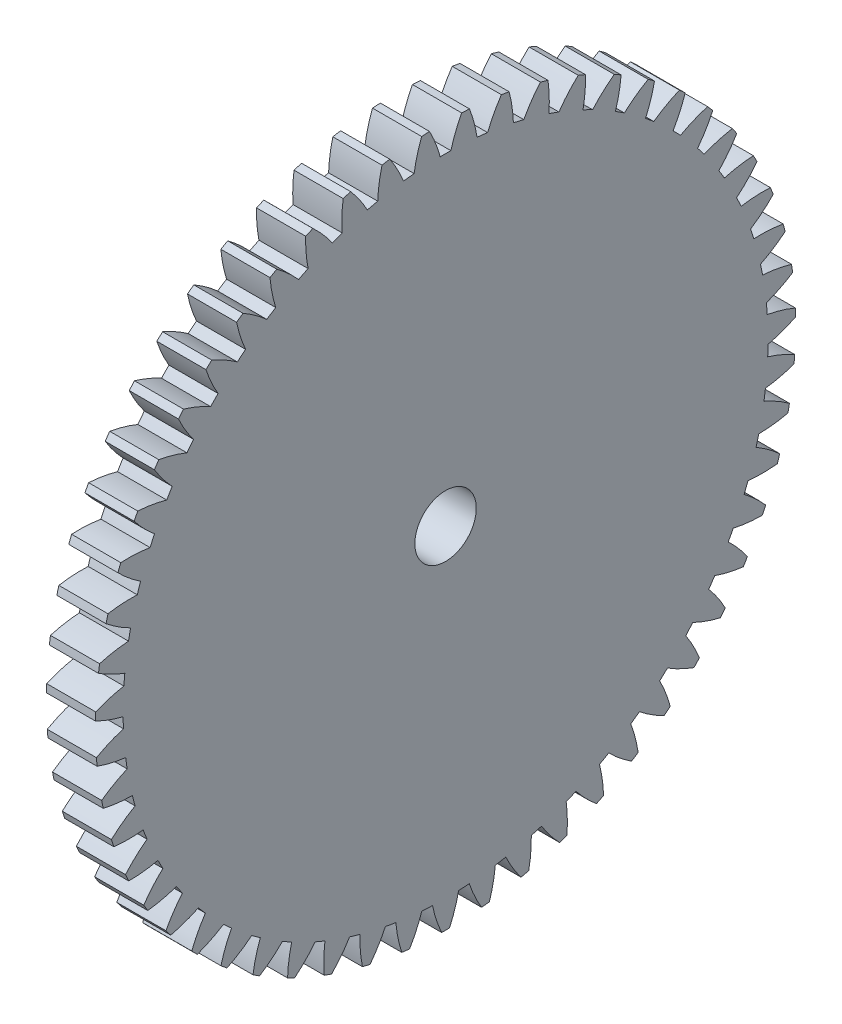
SolidWorks part; units mm, degrees
ref_plane "Plane1" through (0, 0, 0) normal (0, 0, 1) x (1, 0, 0)
ref_plane "Plane2" through (0, 0, 0) normal (0, 1, 0) x (1, 0, 0)
ref_plane "Plane3" through (0, 0, 0) normal (1, 0, 0) x (0, 0, -1)
sketch "HoldingSke" plane through (0, 0, 0) normal (0, 1, 0) x (1, 0, 0)
  line L0 (0, 0) -> (0.5736, -0.8192)
  line L1 (-15, 0) -> (100, 0) construction
  line L2 (0, 0) -> (-2.1039, 2.3779)
  line L3 (0, 0) -> (-11.863, 4.5341)
  line L4 (0, 0) -> (4.9534, 7.0742)
  line L5 (0, 0) -> (-46.8476, -17.4728)
  line L6 (0, 0) -> (-3.3159, -2.2372)
  line L7 (-2.1039, 2.3779) -> (8.6586, 51.2059)
  line L8 (-76.2, 54.61) -> (-75.3, 54.61)
  line L9 (-71.009, 38.7566) -> (-53.1078, 45.2721)
  line L10 (-76.2, 71.12) -> (104.1128, 71.12)
  line L11 (0, 0) -> (-4, 0)
  line L12 (-76.2, 101.6) -> (-76.162, 101.6)
  line L13 (24.9733, 27.94) -> (52.9518, 28.4284)
  line L14 (24.9733, 27.94) -> (24.9743, 27.94)
  line L15 (24.9733, 27.94) -> (100.4006, 29.5858)
  line L16 (-63.627, -1) -> (-12.827, -1)
  circle A0 centre (0, 0) radius 2.5
  circle A1 centre (0, 0) radius 26.249
  circle A2 centre (0, 0) radius 37.5
  circle A3 centre (0, 0) radius 2.5
  dimension "MHD" = 52.498
  dimension "Hub_dia" = 75
  dimension "Bore" = 5
  dimension "MBD" = 5
  dimension "Num_teeth" = 55
  dimension "Pitch" = 1
  dimension "Overall_len" = 50
  dimension "Show_teeth" = 55
  dimension "Thickness" = 4
  dimension "OAL" = 50.0001
  dimension "T_dim" = 0.9
  dimension "Ap" = 20
  dimension "H" = 19.05
  dimension "Pitch_radius" = 180.3128
  dimension "Width" = 4
  dimension "Backlash" = 0.038
  dimension "Addendum_fac" = 1
  dimension "Dedendum_fac" = 1.25
  dimension "Clearance_fac" = 0.25
  dimension "Dedendum_add" = 0.001
  dimension "Module" = 1
sketch "BasProSke" plane through (0, 0, 0) normal (0, 1, 0) x (1, 0, 0)
  line L0 (-10, 0) -> (60, 0) construction
  line L1 (0, 0) -> (0, 28.5)
  line L2 (0, 0) -> (4, 0)
  line L3 (4, 0) -> (4, 28.5)
  line L4 (4, 28.5) -> (0, 28.5)
  dimension "Thickness" = 4
  dimension "Diameter" = 57
revolve "Base-Revolve" add sketch "BasProSke" angle 360 about L0
sketch "TooCutSke" plane through (0, 0, 0) normal (1, 0, 0) x (0, 0, -1)
  line L1 (0, 0) -> (0, 107) construction
  line L2 (0, 0) -> (-0.8518, 27.4868) construction
  line L3 (0, 0) -> (-3.1388, 54.8915) construction
  line L4 (-0.8518, 27.4868) -> (-1.5694, 27.4458) construction
  arc A0 (0.4336, 26.2454) -> (-0.4336, 26.2454) centre (0, 0) ccw
  arc A1 (1.3203, 28.4948) -> (-1.3203, 28.4948) centre (0, 0) ccw
  circle A2 centre (0, 0) radius 27.5 construction
  circle A3 centre (0, 0) radius 25.8415 construction
  arc A4 (-0.4336, 26.2454) -> (-1.3203, 28.4948) centre (-11.0486, 23.3605) ccw
  arc A5 (1.3203, 28.4948) -> (0.4336, 26.2454) centre (11.0486, 23.3605) ccw
  dimension "Root_dia" = 52.498
  dimension "Overcut_dia" = 57.0508
  dimension "Pitch_dia" = 55
  dimension "Base_dia" = 51.6831
  dimension "Flank_rad" = 11
  dimension "Half_ang" = 3.273
  dimension "Half_CT" = 0.7188
extrude "ToothCut" cut sketch "TooCutSke" along normal through all
fillet "Breaks" [suppressed] radius 0.02
fillet "RootFillets" [suppressed] radius 0.251
pattern_circular "TeethCuts" count 55 every 6.545 about axis through (-10, 0, 0) along (1, 0, 0) of "ToothCut", "RootFillets", "Breaks"
sketch "HubNeaOneSke" plane through (0, 0, 0) normal (-1, 0, 0) x (0, 0, 1)
  circle A0 centre (0, 0) radius 26.249
  dimension "Diameter" = 52.498
extrude "HubNearOne" [suppressed] add sketch "HubNeaOneSke" along normal blind 46.0001
sketch "HubNeaBotSke" plane through (0, 0, 0) normal (-1, 0, 0) x (0, 0, 1)
  circle A0 centre (0, 0) radius 26.249
  dimension "Diameter" = 52.498
extrude "HubNearBoth" [suppressed] add sketch "HubNeaBotSke" along normal blind 23
ref_plane "FarPln" through (4, 0, 0) normal (1, 0, 0) x (0, 0, -1)
sketch "HubFarSke" plane through (4, 0, 0) normal (1, 0, 0) x (0, 0, -1)
  circle A0 centre (0, 0) radius 26.249
  dimension "Diameter" = 52.498
extrude "HubFar" [suppressed] add sketch "HubFarSke" along normal blind 23
sketch "BorSke" plane through (0, 0, 0) normal (1, 0, 0) x (0, 0, -1)
  circle A0 centre (0, 0) radius 2.5
  dimension "Diameter" = 5
extrude "Bore" cut sketch "BorSke" along normal mid plane 100.0001
sketch "KeySke" plane through (0, 0, 0) normal (1, 0, 0) x (0, 0, -1)
  line L0 (-1, 0) -> (-1, 3.4)
  line L1 (-1, 3.4) -> (1, 3.4)
  line L2 (1, 3.4) -> (1, 0)
  line L3 (0, 0) -> (0, 34) construction
  line L4 (-1, 0) -> (1, 0)
  dimension "Offset" = 3.4
  dimension "Width" = 2
extrude "Keyway" [suppressed] cut sketch "KeySke" along normal mid plane 100.0001
pattern_circular "Keyway2" [suppressed] count 2 every 90 about axis through (-10, 0, 0) along (1, 0, 0)
equation "' \"Module@HoldingSke\" = 6.35"
equation "' \"Num_teeth@HoldingSke\" = 12"
equation "' \"Ap@HoldingSke\" =  20"
equation "' \"Ap@HoldingSke\" = 20"
equation "' \"Width@HoldingSke\" = 0.5 * 25.4"
equation "' \"Hub_dia@HoldingSke\"= 1 * 25.4"
equation "' \"Hub_dia@HoldingSke\" = 1 * 25.4"
equation "' \"Overall_len@HoldingSke\" = 1.0 * 25.4"
equation "' \"Bore@HoldingSke\" = 0.75 * 25.4"
equation "' \"T_dim@HoldingSke\" = 0.1 * 25.4"
equation "' \"Width@KeySke\" = 0.25 * 25.4"
equation "' \"Show_teeth@HoldingSke\" = 13"
equation "' \"Backlash@HoldingSke\" = 0.009 * 25.4"
equation "' \"Addendum_fac@HoldingSke\" = 1.0"
equation "' \"Dedendum_fac@HoldingSke\" = 1.25"
equation "' \"Dedendum_add@HoldingSke\" = 0.00005 * 25.4"
equation "' \"Clearance_fac@HoldingSke\" = 0.25"
equation "\"Pitch@HoldingSke\" = 1 / \"Module@HoldingSke\""
equation "\"Overcut_dia@TooCutSke\" = (\"Num_teeth@HoldingSke\" + 2 * \"Addendum_fac@HoldingSke\") / \"Pitch@HoldingSke\" + 0.002 * 25.4"
equation "\"Pitch_dia@TooCutSke\" = \"Num_teeth@HoldingSke\" / \"Pitch@HoldingSke\""
equation "\"Base_dia@TooCutSke\" = \"Num_teeth@HoldingSke\" / \"Pitch@HoldingSke\" * cos((\"Ap@HoldingSke\"  * 3.14159265 / 180))"
equation "\"Root_dia@TooCutSke\" = (\"Num_teeth@HoldingSke\" + 2) / \"Pitch@HoldingSke\" - 2 * (\"Addendum_fac@HoldingSke\" + \"Dedendum_fac@HoldingSke\") / \"Pitch@HoldingSke\" - \"Dedendum_add@HoldingSke\" * 2"
equation "\"Half_ang@TooCutSke\" = 180 / \"Num_teeth@HoldingSke\""
equation "\"Half_CT@TooCutSke\" = \"Num_teeth@HoldingSke\" / \"Pitch@HoldingSke\" * sin((3.14159265 / 2 / \"Num_teeth@HoldingSke\")) / 2 - 7 * \"Backlash@HoldingSke\" / 4"
equation "\"Flank_rad@TooCutSke\" = \"Num_teeth@HoldingSke\" / \"Pitch@HoldingSke\" / 5"
equation "\"Radius@RootFillets\" = \"Clearance_fac@HoldingSke\" / \"Pitch@HoldingSke\" + \"Dedendum_add@HoldingSke\""
equation "\"Break_rad@Breaks\" = 0.02 / \"Pitch@HoldingSke\""
equation "\"Thickness@HoldingSke\" = \"Width@HoldingSke\""
equation "\"OAL@HoldingSke\" = \"Thickness@HoldingSke\""
equation "\"MHD@HoldingSke\" = (\"Num_teeth@HoldingSke\" + 2) / \"Pitch@HoldingSke\" - 2 * (\"Addendum_fac@HoldingSke\" + \"Dedendum_fac@HoldingSke\")  / \"Pitch@HoldingSke\" - \"Dedendum_add@HoldingSke\" * 2"
equation "\"MBD@HoldingSke\" = (\"Num_teeth@HoldingSke\" + 2) / \"Pitch@HoldingSke\" - 2 * (\"Addendum_fac@HoldingSke\" + \"Dedendum_fac@HoldingSke\")  / \"Pitch@HoldingSke\" - \"Dedendum_add@HoldingSke\" * 2 - 0.002 * 25.4"
equation "\"MHD@HoldingSke\" = ((sgn( \"MHD@HoldingSke\" - \"Hub_dia@HoldingSke\" )-1)*( \"MHD@HoldingSke\" - \"Hub_dia@HoldingSke\" ))/-2+ \"Hub_dia@HoldingSke\""
equation "\"MBD@HoldingSke\" = ((sgn( \"MBD@HoldingSke\" - \"Bore@HoldingSke\" )-1)*( \"MBD@HoldingSke\" - \"Bore@HoldingSke\" ))/-2+ \"Bore@HoldingSke\""
equation "\"OAL@HoldingSke\" = ((sgn( \"OAL@HoldingSke\" - \"Overall_len@HoldingSke\" )+1)*( \"OAL@HoldingSke\" - \"Overall_len@HoldingSke\" ))/2 + \"Overall_len@HoldingSke\" + 0.000002 * 25.4"
equation "\"Num_teeth@TeethCuts\" = int( \"Show_teeth@HoldingSke\" ) + 1"
equation "\"Num_teeth@TeethCuts\" = ((sgn( \"Num_teeth@TeethCuts\" - \"Num_teeth@HoldingSke\" )-1)*( \"Num_teeth@TeethCuts\" - \"Num_teeth@HoldingSke\" ))/-2+ \"Num_teeth@HoldingSke\""
equation "\"Num_teeth@TeethCuts\" = ((sgn( \"Num_teeth@TeethCuts\" - 2.0)+1)*( \"Num_teeth@TeethCuts\" - 2.0))/2 +2.0"
equation "\"Angle@TeethCuts\" = 360.0 / \"Num_teeth@HoldingSke\""
equation "\"Diameter@BasProSke\" = (\"Num_teeth@HoldingSke\" + 2 * \"Addendum_fac@HoldingSke\") / \"Pitch@HoldingSke\""
equation "\"Thickness@BasProSke\"  = \"Thickness@HoldingSke\""
equation "' \"Fillet_rad@BasProSke\" =  \"Thickness@HoldingSke\" * 0.05"
equation "' \"Fillet_rad@BasProSke\" = \"Thickness@HoldingSke\" * 0.05"
equation "\"MHD@HoldingSke\" = ((sgn( \"MHD@HoldingSke\" - \"Root_dia@TooCutSke\" )-1)*( \"MHD@HoldingSke\" - \"Root_dia@TooCutSke\" ))/-2+ \"Root_dia@TooCutSke\""
equation "\"Diameter@HubNeaOneSke\" = \"MHD@HoldingSke\""
equation "\"Length@HubNearOne\" = \"OAL@HoldingSke\" - \"Thickness@BasProSke\""
equation "\"Diameter@HubNeaBotSke\" = \"MHD@HoldingSke\""
equation "\"Length@HubNearBoth\" = ( \"OAL@HoldingSke\" - \"Thickness@BasProSke\" ) / 2.0"
equation "\"Thickness@FarPln\" = \"Thickness@BasProSke\""
equation "\"Diameter@HubFarSke\" = \"MHD@HoldingSke\""
equation "\"Length@HubFar\" = ( \"OAL@HoldingSke\" - \"Thickness@BasProSke\" ) / 2.0"
equation "\"Diameter@BorSke\" = \"MBD@HoldingSke\""
equation "\"D1@Bore\" = \"OAL@HoldingSke\" * 2.0"
equation "\"D1@Keyway\" = \"OAL@HoldingSke\" * 2.0"
equation "\"Offset@KeySke\" = \"T_dim@HoldingSke\" + \"MBD@HoldingSke\" / 2.0"
